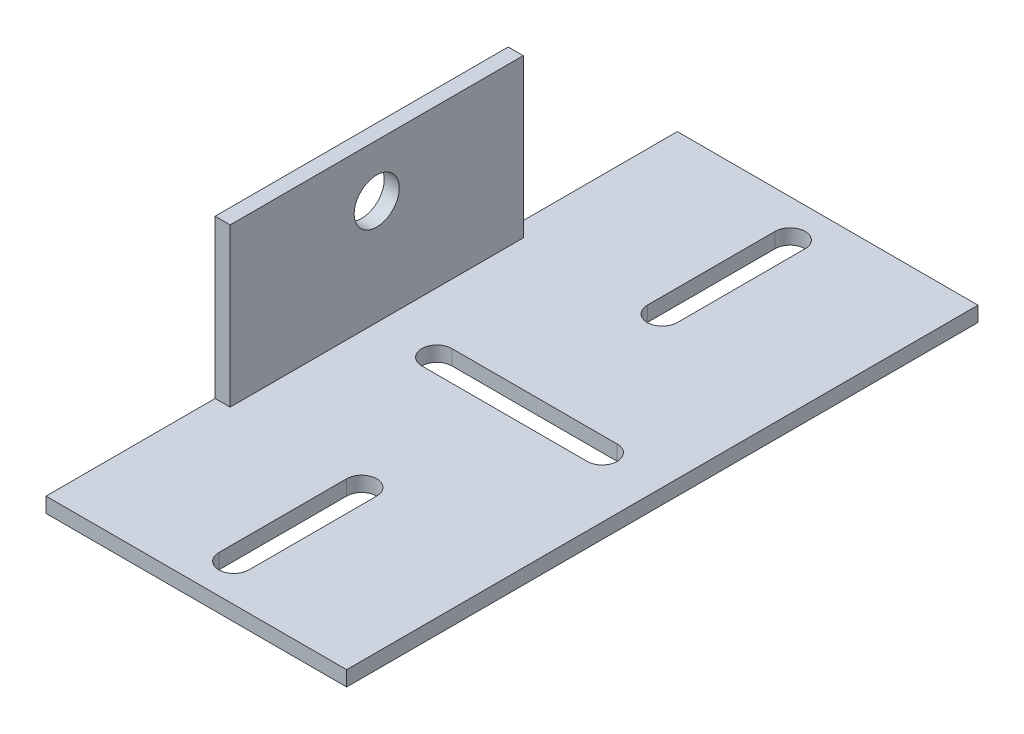
SolidWorks part; units mm, degrees
ref_plane "Спереди" through (0, 0, 0) normal (0, 0, 1) x (1, 0, 0)
ref_plane "Сверху" through (0, 0, 0) normal (0, 1, 0) x (1, 0, 0)
ref_plane "Справа" through (0, 0, 0) normal (1, 0, 0) x (0, 0, -1)
sketch "Эскиз2" plane through (0, 0, 0) normal (0, 0, 1) x (1, 0, 0)
  line L0 (0, 23) -> (0, 0)
  line L1 (0, 0) -> (40, 0)
extrude "Вытянуть-Тонкостенный1" add sketch "Эскиз2" along normal blind 84 thin thin type one direction reverse wall 2
sketch "Эскиз3" plane through (0, 2, 0) normal (0, 1, 0) x (1, 0, 0)
  line L0 (32, -40) -> (10, -40)
  line L1 (32, -44) -> (10, -44)
  line L2 (18, -5) -> (18, -22)
  line L3 (22, -5) -> (22, -22)
  line L4 (40, -42) -> (2, -42) construction
  line L5 (40, -84) -> (40, 0) construction
  line L6 (2, -84) -> (2, 0) construction
  line L7 (22, -79) -> (22, -62)
  line L8 (18, -79) -> (18, -62)
  arc A0 (32, -40) -> (32, -44) centre (32, -42) cw
  arc A1 (10, -40) -> (10, -44) centre (10, -42) ccw
  arc A2 (18, -5) -> (22, -5) centre (20, -5) cw
  arc A3 (18, -22) -> (22, -22) centre (20, -22) ccw
  arc A4 (18, -62) -> (22, -62) centre (20, -62) cw
  arc A5 (18, -79) -> (22, -79) centre (20, -79) ccw
  dimension "D1" = 20
extrude "Вырез-Вытянуть1" cut sketch "Эскиз3" against normal blind 10
sketch "Эскиз4" plane through (0, 0, 0) normal (-1, 0, 0) x (0, 0, 1)
  line L0 (42, 23) -> (42, 0) construction
  line L1 (84, 23) -> (0, 23) construction
  circle A0 centre (42, 16) radius 3
extrude "Вырез-Вытянуть2" cut sketch "Эскиз4" against normal blind 10
sketch "Эскиз5" plane through (0, 0, 0) normal (-1, 0, 0) x (0, 0, 1)
  line L0 (42, 23) -> (42, -0.8996) construction
  line L1 (0, 23) -> (22.5, 23)
  line L2 (0, 23) -> (0, 2)
  line L3 (0, 2) -> (22.5, 2)
  line L4 (22.5, 23) -> (22.5, 2)
  line L5 (84, 23) -> (0, 23) construction
  line L6 (61.5, 23) -> (61.5, 2)
  line L7 (84, 2) -> (61.5, 2)
  line L8 (84, 23) -> (84, 2)
  line L9 (84, 23) -> (61.5, 23)
extrude "Вырез-Вытянуть3" cut sketch "Эскиз5" against normal blind 10
